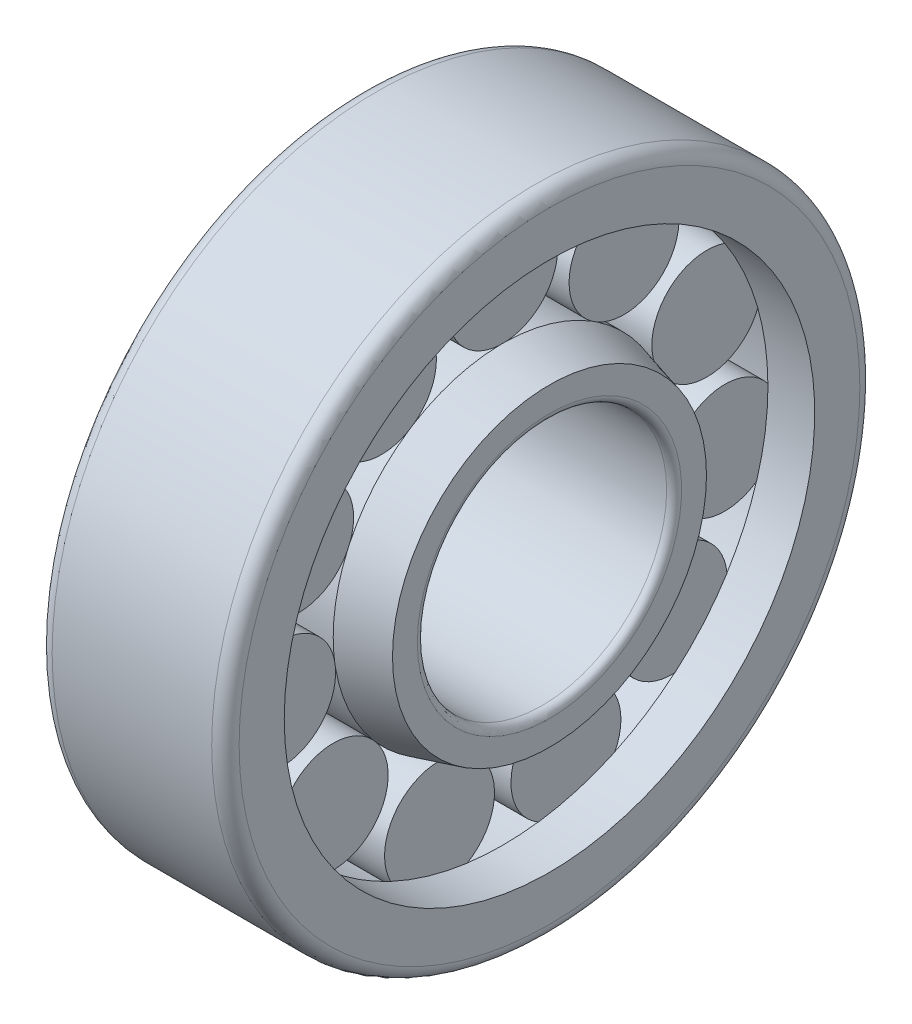
SolidWorks part; units mm, degrees
ref_plane "Front" through (0, 0, 0) normal (0, 0, 1) x (1, 0, 0)
ref_plane "Top" through (0, 0, 0) normal (0, 1, 0) x (1, 0, 0)
ref_plane "Right" through (0, 0, 0) normal (1, 0, 0) x (0, 0, -1)
sketch "Sketch1" plane through (0, 0, 0) normal (0, 0, 1) x (1, 0, 0)
  line L0 (-7.5, 10) -> (7.5, 10)
  line L1 (7.5, 10) -> (7.5, 12.5952)
  line L2 (7.5, 12.5952) -> (3.75, 13.6)
  line L3 (3.75, 13.6) -> (-3.75, 13.6)
  line L4 (-3.75, 13.6) -> (-7.5, 12.5952)
  line L5 (-7.5, 12.5952) -> (-7.5, 10)
  line L6 (-10.1379, 0) -> (10.5422, 0) construction
  dimension "B" = 15
  dimension "d" = 20
  dimension "FW" = 27.2
  dimension "D5" = 15
  dimension "D6" = 15
  dimension "D7" = 7.5
  dimension "D2" = 7.5
  dimension "D8" = 3.75
revolve "Revolve1" add sketch "Sketch1" angle 360 about L6
sketch "Sketch2" plane through (0, 0, 0) normal (0, 0, 1) x (1, 0, 0)
  line L0 (-3.75, 13.59) -> (3.75, 13.59)
  line L1 (3.75, 13.59) -> (3.75, 18)
  line L2 (-3.75, 18) -> (3.75, 18)
  line L3 (-3.75, 18) -> (-3.75, 13.59)
  line L4 (-7.1198, 0) -> (7.769, 0) construction
  line L6 (-7.4228, 18) -> (7.769, 18) construction
  dimension "D1" = 27.18
  dimension "D2" = 18
  dimension "D4" = 7.5
  dimension "D5" = 3.75
revolve "Revolve2" add sketch "Sketch2" angle 360 about L6
sketch "Sketch3" plane through (0, 0, 0) normal (0, 0, 1) x (1, 0, 0)
  line L0 (-7.5, 26) -> (7.5, 26)
  line L1 (7.5, 26) -> (7.5, 21.28)
  line L2 (7.5, 21.28) -> (3.74, 21.28)
  line L3 (3.74, 21.28) -> (3.74, 22.4)
  line L4 (3.74, 22.4) -> (-3.74, 22.4)
  line L5 (-3.74, 22.4) -> (-3.74, 21.28)
  line L6 (-3.74, 21.28) -> (-7.5, 21.28)
  line L7 (-7.5, 21.28) -> (-7.5, 26)
  line L8 (-9.0822, 0) -> (10.5352, 0) construction
  dimension "B" = 15
  dimension "DD" = 52
  dimension "D2" = 44.8
  dimension "D3" = 42.56
  dimension "D6" = 7.48
  dimension "D7" = 3.74
  dimension "D5" = 7.5
revolve "Revolve3" add sketch "Sketch3" angle 360 about L8
pattern_circular "Circular-Pattern1" count 11 over 360 about axis through (0, 0, 0) along (1, 0, 0) of "Revolve2"
fillet "Fillet1" radius 1.1 2 edges at (-7.5, 0, 26) (7.5, 0, 26)
fillet "Fillet2" radius 0.6 2 edges at (7.5, 0, 10) (-7.5, 0, 10)
equation "\"D2@Sketch1\" = \"B@Sketch1\" / 2"
equation "\"D7@Sketch1\" = \"D2@Sketch1\""
equation "\"D8@Sketch1\" = \"D7@Sketch1\"/2"
equation "\"D2@Sketch2\" = ( \"DD@Sketch3\" + \"d@Sketch1\" )  / 4"
equation "\"D4@Sketch2\" = \"B@Sketch1\" / 2"
equation "\"D5@Sketch2\" = \"D4@Sketch2\" / 2"
equation "\"D1@Sketch2\" = \"FW@Sketch1\" - 0.02"
equation "\"B@Sketch3\" = \"B@Sketch1\""
equation "\"D5@Sketch3\" = \"B@Sketch3\" / 2"
equation "\"D6@Sketch3\" = \"D5@Sketch3\" - 0.02"
equation "\"D7@Sketch3\" = \"D6@Sketch3\" / 2"
equation "\"D2@Sketch3\" = ( \"DD@Sketch3\" + \"d@Sketch1\" )  / 4 * 2 + ( ( \"DD@Sketch3\" + \"d@Sketch1\" )  / 4 * 2 - \"FW@Sketch1\"  ) "
equation "\"D3@Sketch3\" = \"D2@Sketch3\" * 0.95"
equation "\"m@Circular-Pattern1\"=int(3.14159265/atn(((\"DD@Sketch3\"+\"d@Sketch1\")/4-\"FW@Sketch1\"/2+0.02) / sqr((\"DD@Sketch3\"+\"d@Sketch1\")/4  * (\"DD@Sketch3\"+\"d@Sketch1\")/4 - ((\"DD@Sketch3\"+\"d@Sketch1\")/4-\"FW@Sketch1\"/2+0.02) *  ((\"DD@Sketch3\"+\"d@Sketch1\")/4-\"FW@Sketch1\"/2+0.02))))-1"
